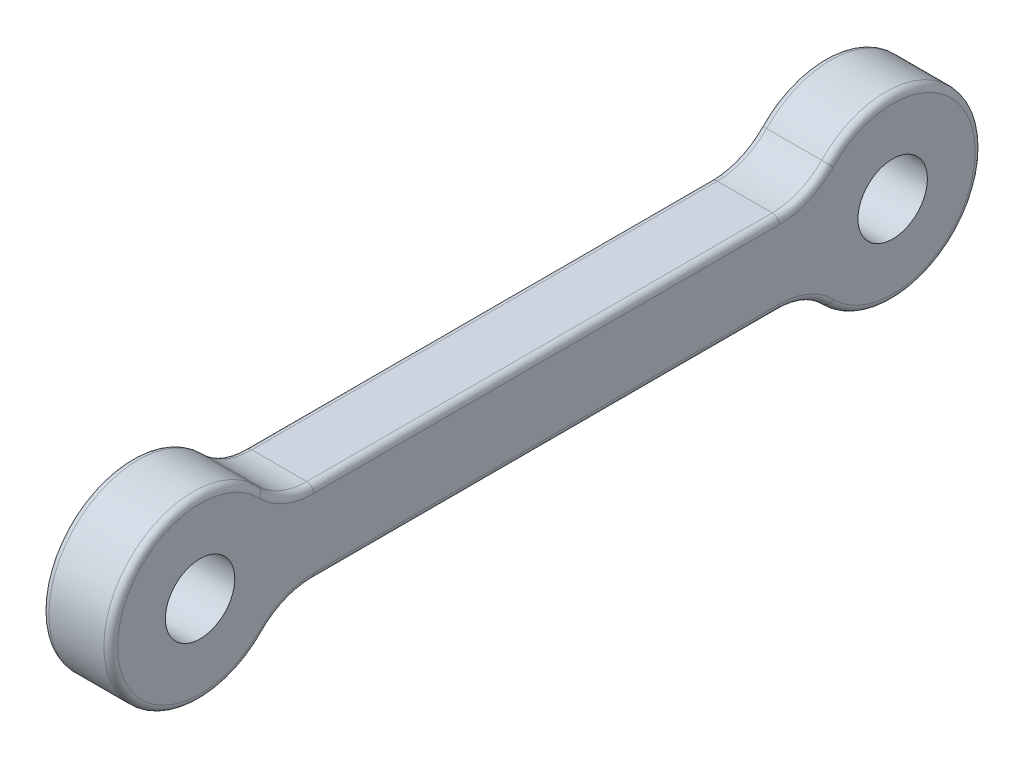
SolidWorks part; units mm, degrees
ref_plane "前视基准面" through (0, 0, 0) normal (0, 0, 1) x (1, 0, 0)
ref_plane "上视基准面" through (0, 0, 0) normal (0, 1, 0) x (1, 0, 0)
ref_plane "右视基准面" through (0, 0, 0) normal (1, 0, 0) x (0, 0, -1)
sketch "草图1" plane through (0, 0, 0) normal (1, 0, 0) x (0, 0, -1)
  line L0 (-100.75, 0) -> (0, 0) construction
  line L1 (-84.2273, 6) -> (-16.5227, 6)
  line L2 (-84.2273, -6) -> (-16.5227, -6)
  arc A0 (-91.4111, 9.0435) -> (-91.4111, -9.0435) centre (-100.75, 0) ccw
  arc A1 (-9.3389, -9.0435) -> (-9.3389, 9.0435) centre (0, 0) ccw
  circle A2 centre (-100.75, 0) radius 5.05
  circle A3 centre (0, 0) radius 5.05
  arc A4 (-16.5227, -6) -> (-9.3389, -9.0435) centre (-16.5227, -16) cw
  arc A5 (-16.5227, 6) -> (-9.3389, 9.0435) centre (-16.5227, 16) ccw
  arc A6 (-84.2273, -6) -> (-91.4111, -9.0435) centre (-84.2273, -16) ccw
  arc A7 (-84.2273, 6) -> (-91.4111, 9.0435) centre (-84.2273, 16) cw
  dimension "D1" = 100.75
  dimension "D3" = 10.1
  dimension "D5" = 10
  dimension "D2" = 13
  dimension "D4" = 12
extrude "凸台-拉伸1" add sketch "草图1" along normal blind 10
fillet "圆角1" radius 1 16 edges at (0, 6.7923, 12.6218) (0, 0, -13) (0, -6.7923, 12.6218) (0, -6, 50.375) (0, -6.7923, 88.1282) (0, 0, 113.75) (0, 6.7923, 88.1282) (10, 6.7923, 88.1282) (10, 6, 50.375) (10, 6.7923, 12.6218) (10, 0, -13) (10, -6.7923, 12.6218) (10, -6, 50.375) (10, -6.7923, 88.1282) (0, 6, 50.375) (10, 0, 113.75)
